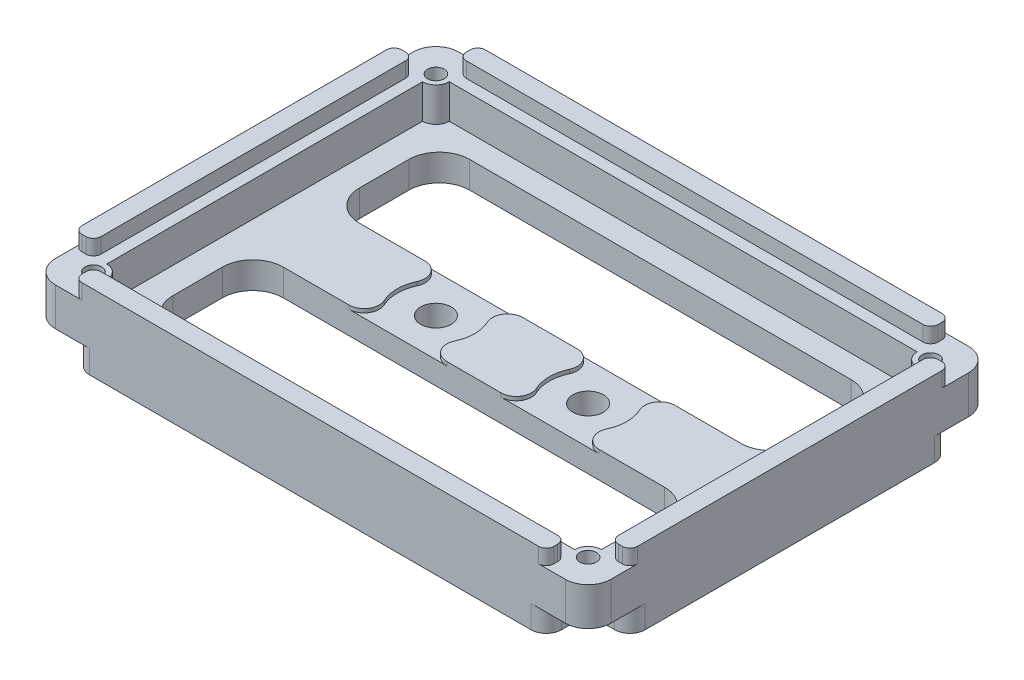
SolidWorks part; units mm, degrees
ref_plane "Plan de face" through (0, 0, 0) normal (0, 0, 1) x (1, 0, 0)
ref_plane "Plan de dessus" through (0, 0, 0) normal (0, 1, 0) x (1, 0, 0)
ref_plane "Plan de droite" through (0, 0, 0) normal (1, 0, 0) x (0, 0, -1)
sketch "Esquisse1" plane through (0, 0, 0) normal (0, 1, 0) x (1, 0, 0)
  line L1 (-32.5, -22.5) -> (32.5, -22.5) construction
  line L2 (-32.5, -22.5) -> (-32.5, 22.5) construction
  line L3 (-32.5, 22.5) -> (32.5, 22.5) construction
  line L4 (32.5, -22.5) -> (32.5, 22.5) construction
  line L5 (-32.5, -22.5) -> (32.5, 22.5) construction
  line L6 (-32.5, 22.5) -> (32.5, -22.5) construction
  line L7 (-31.0556, -21.5) -> (31.0556, -21.5)
  line L8 (-31.0556, -21.5) -> (-31.0556, 21.5)
  line L9 (-31.0556, 21.5) -> (31.0556, 21.5)
  line L10 (31.0556, -21.5) -> (31.0556, 21.5)
  line L11 (-31.0556, -21.5) -> (31.0556, 21.5) construction
  line L12 (-31.0556, 21.5) -> (31.0556, -21.5) construction
  line L13 (-36.5, -26.5) -> (36.5, -26.5)
  line L14 (-36.5, -26.5) -> (-36.5, 26.5)
  line L15 (-36.5, 26.5) -> (36.5, 26.5)
  line L16 (36.5, -26.5) -> (36.5, 26.5)
  line L17 (-36.5, -26.5) -> (36.5, 26.5) construction
  line L18 (-36.5, 26.5) -> (36.5, -26.5) construction
  circle A0 centre (-32.5, 22.5) radius 1.1
  circle A1 centre (32.5, 22.5) radius 1.1
  circle A2 centre (32.5, -22.5) radius 1.1
  circle A3 centre (-32.5, -22.5) radius 1.1
  point P0 (0, 0)
  point P10 (0, 0)
  point P15 (0, 0)
  dimension "D3" = 2.2
  dimension "D1" = 65
  dimension "D2" = 45
  dimension "D4" = 1
  dimension "D5" = 4
  dimension "D6" = 4
extrude "Boss.-Extru.1" add sketch "Esquisse1" along normal blind 10
sketch "Esquisse2" plane through (0, 0, 0) normal (0, -1, 0) x (1, 0, 0)
  line L1 (-36.5, -26.5) -> (36.5, -26.5)
  line L2 (-36.5, -26.5) -> (-36.5, 26.5)
  line L3 (-36.5, 26.5) -> (36.5, 26.5)
  line L4 (36.5, -26.5) -> (36.5, 26.5)
  line L5 (-36.5, -26.5) -> (36.5, 26.5) construction
  line L6 (-36.5, 26.5) -> (36.5, -26.5) construction
  point P0 (0, 0)
extrude "Boss.-Extru.2" add sketch "Esquisse2" against normal blind 4
sketch "Esquisse3" plane through (0, 0, 0) normal (0, -1, 0) x (1, 0, 0)
  line L1 (-36.5, 26.5) -> (-31, 26.5)
  line L2 (-36.5, 26.5) -> (-36.5, 21)
  line L3 (-36.5, 21) -> (-31, 21)
  line L4 (-31, 26.5) -> (-31, 21)
  line L5 (36.5, 26.5) -> (31, 26.5)
  line L6 (36.5, 26.5) -> (36.5, 21)
  line L7 (36.5, 21) -> (31, 21)
  line L8 (31, 26.5) -> (31, 21)
  line L9 (36.5, -26.5) -> (31, -26.5)
  line L10 (36.5, -26.5) -> (36.5, -21)
  line L11 (36.5, -21) -> (31, -21)
  line L12 (31, -26.5) -> (31, -21)
  line L13 (-36.5, -26.5) -> (-31, -26.5)
  line L14 (-36.5, -26.5) -> (-36.5, -21)
  line L15 (-36.5, -21) -> (-31, -21)
  line L16 (-31, -26.5) -> (-31, -21)
  dimension "D1" = 5.5
extrude "Enlèv. mat.-Extru.1" cut sketch "Esquisse3" against normal blind 3
sketch "Esquisse4" plane through (0, 4, 0) normal (0, 1, 0) x (1, 0, 0)
  circle A0 centre (-32.5, 22.5) radius 1.1
  circle A1 centre (32.5, 22.5) radius 1.1
  circle A2 centre (32.5, -22.5) radius 1.1
  circle A3 centre (-32.5, -22.5) radius 1.1
  dimension "D1" = 2.2
extrude "Enlèv. mat.-Extru.2" cut sketch "Esquisse4" against normal blind 5
fillet "Congé3" radius 3 4 edges at (-36.5, 6.5, 26.5) (-36.5, 6.5, -26.5) (36.5, 6.5, -26.5) (36.5, 6.5, 26.5)
sketch "Esquisse5" plane through (0, 4, 0) normal (0, 1, 0) x (1, 0, 0)
  line L0 (-10, 0) -> (10, 0) construction
  line L1 (31.0556, 21.5) -> (-31.0556, 21.5) construction
  line L2 (-29.0556, 5) -> (29.0556, 5)
  line L3 (-29.0556, 5) -> (-29.0556, 19.5)
  line L4 (-29.0556, 19.5) -> (29.0556, 19.5)
  line L5 (29.0556, 5) -> (29.0556, 19.5)
  line L6 (-29.0556, 5) -> (29.0556, 19.5) construction
  line L7 (-29.0556, 19.5) -> (29.0556, 5) construction
  line L8 (-29.0556, -5) -> (29.0556, -5)
  line L9 (-29.0556, -5) -> (-29.0556, -19.5)
  line L10 (-29.0556, -19.5) -> (29.0556, -19.5)
  line L11 (29.0556, -5) -> (29.0556, -19.5)
  line L12 (-29.0556, -5) -> (29.0556, -19.5) construction
  line L13 (-29.0556, -19.5) -> (29.0556, -5) construction
  line L14 (-31.0556, -21.5) -> (31.0556, -21.5) construction
  line L15 (-31.0556, 21.5) -> (-31.0556, -21.5) construction
  line L16 (31.0556, -21.5) -> (31.0556, 21.5) construction
  line L17 (31.0556, -21.5) -> (31.0556, 21.5) construction
  circle A0 centre (-10, 0) radius 2
  circle A1 centre (10, 0) radius 2
  point P3 (0, 0)
  point P6 (0, 12.25)
  point P11 (0, -12.25)
  dimension "D1" = 4
  dimension "D2" = 2
  dimension "D3" = 2
  dimension "D4" = 2
  dimension "D5" = 2
  dimension "D6" = 2
  dimension "D7" = 2
  dimension "D8" = 5
  dimension "D9" = 5
  dimension "D10" = 20
extrude "Enlèv. mat.-Extru.3" cut sketch "Esquisse5" against normal blind 5
fillet "Congé4" radius 4 8 edges at (-29.0556, 2, 19.5) (29.0556, 2, 5) (29.0556, 2, 19.5) (-29.0556, 2, 5) (29.0556, 2, -5) (29.0556, 2, -19.5) (-29.0556, 2, -19.5) (-29.0556, 2, -5)
fillet "Congé5" radius 2 12 edges at (-31, 1.5, -21) (-31, 1.5, 21) (31, 1.5, 21) (31, 1.5, -21) (-36.5, 1.5, 21) (-31, 1.5, 26.5) (31, 1.5, 26.5) (36.5, 1.5, 21) (36.5, 1.5, -21) (31, 1.5, -26.5) (-31, 1.5, -26.5) (-36.5, 1.5, -21)
sketch "Esquisse6" plane through (0, 4, 0) normal (0, 1, 0) x (1, 0, 0)
  circle A0 centre (-10, 0) radius 5.1
  circle A1 centre (10, 0) radius 5.1
  dimension "D1" = 10.2
extrude "Enlèv. mat.-Extru.6" cut sketch "Esquisse6" against normal blind 1
fillet "Congé6" radius 2 8 edges at (11.005, 3.5, 5) (8.995, 3.5, 5) (8.995, 3.5, -5) (11.005, 3.5, -5) (-11.005, 3.5, 5) (-8.995, 3.5, 5) (-8.995, 3.5, -5) (-11.005, 3.5, -5)
sketch "Esquisse7" plane through (0, 10, 0) normal (0, 1, 0) x (1, 0, 0)
  line L0 (-32.5, 20.7432) -> (-32.5, -20.7432)
  line L2 (-30.7432, -22.5) -> (30.7432, -22.5)
  line L4 (32.5, -20.7432) -> (32.5, 20.7432)
  line L6 (30.7432, 22.5) -> (-30.7432, 22.5)
  circle A0 centre (-32.5, 22.5) radius 1.7568 construction
  circle A1 centre (32.5, 22.5) radius 1.7568 construction
  circle A2 centre (-32.5, -22.5) radius 1.7568 construction
  circle A3 centre (32.5, -22.5) radius 1.7568 construction
  arc A4 (-30.7432, 22.5) -> (-32.5, 20.7432) centre (-32.5, 22.5) cw
  arc A5 (30.7432, 22.5) -> (32.5, 20.7432) centre (32.5, 22.5) ccw
  arc A6 (-32.5, -20.7432) -> (-30.7432, -22.5) centre (-32.5, -22.5) cw
  arc A7 (32.5, -20.7432) -> (30.7432, -22.5) centre (32.5, -22.5) ccw
extrude "Enlèv. mat.-Extru.7" cut sketch "Esquisse7" against normal blind 6.5
sketch "Esquisse8" plane through (0, 10, 0) normal (0, 1, 0) x (1, 0, 0)
  line L1 (-34, -24) -> (34, -24)
  line L2 (-34, -24) -> (-34, 24)
  line L3 (-34, 24) -> (34, 24)
  line L4 (34, -24) -> (34, 24)
  line L5 (-34, -24) -> (34, 24) construction
  line L6 (-34, 24) -> (34, -24) construction
  point P0 (0, 0)
  dimension "D1" = 68
  dimension "D2" = 48
extrude "Enlèv. mat.-Extru.8" cut sketch "Esquisse8" against normal blind 2
sketch "Esquisse9" plane through (0, 10, 0) normal (0, 1, 0) x (-1, 0, 0)
  line L0 (-36.5, 23.5) -> (-36.5, -23.5) construction
  line L1 (-36.5, 26.5) -> (-31, 26.5)
  line L2 (-36.5, 26.5) -> (-36.5, 21)
  line L3 (-36.5, 21) -> (-31, 21)
  line L4 (-31, 26.5) -> (-31, 21)
  line L5 (36.5, 26.5) -> (31, 26.5)
  line L6 (36.5, 26.5) -> (36.5, 21)
  line L7 (36.5, 21) -> (31, 21)
  line L8 (31, 26.5) -> (31, 21)
  line L9 (36.5, -26.5) -> (31, -26.5)
  line L10 (36.5, -26.5) -> (36.5, -21)
  line L11 (36.5, -21) -> (31, -21)
  line L12 (31, -26.5) -> (31, -21)
  line L13 (-36.5, -26.5) -> (-31, -26.5)
  line L14 (-36.5, -26.5) -> (-36.5, -21)
  line L15 (-36.5, -21) -> (-31, -21)
  line L16 (-31, -26.5) -> (-31, -21)
  line L17 (-33.5, -26.5) -> (33.5, -26.5) construction
  line L18 (33.5, 26.5) -> (-33.5, 26.5) construction
  line L19 (36.5, -23.5) -> (36.5, 23.5) construction
  dimension "D1" = 5.5
extrude "Enlèv. mat.-Extru.9" cut sketch "Esquisse9" against normal blind 2
fillet "Congé8" radius 1 16 edges at (-31, 9, 26.5) (-31, 9, 24) (31, 9, 26.5) (31, 9, 24) (36.5, 9, 21) (34, 9, 21) (31, 9, -26.5) (31, 9, -24) (34, 9, -21) (36.5, 9, -21) (-31, 9, -24) (-31, 9, -26.5) (-36.5, 9, -21) (-34, 9, -21) (-36.5, 9, 21) (-34, 9, 21)
